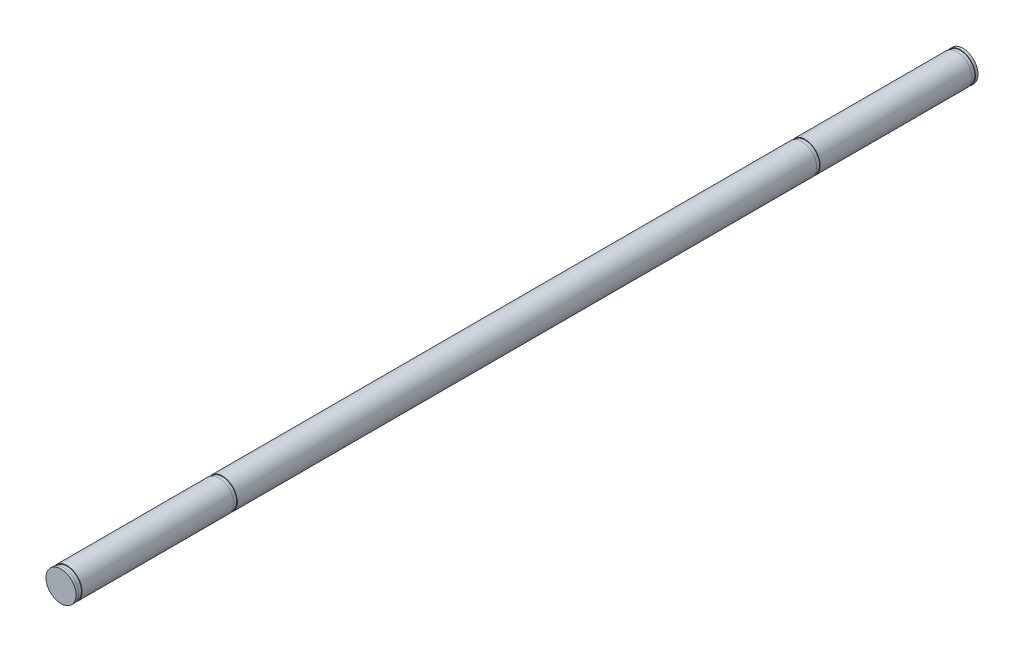
SolidWorks part; units mm, degrees
ref_plane "Front Plane" through (0, 0, 0) normal (0, 0, 1) x (1, 0, 0)
ref_plane "Top Plane" through (0, 0, 0) normal (0, 1, 0) x (1, 0, 0)
ref_plane "Right Plane" through (0, 0, 0) normal (1, 0, 0) x (0, 0, -1)
sketch "Sketch1" plane through (0, 0, 0) normal (0, 0, 1) x (1, 0, 0)
  circle A0 centre (0, 0) radius 5
  dimension "D1" = 10
extrude "Boss-Extrude1" add sketch "Sketch1" along normal mid plane 300
ref_plane "Plane1" through (0, 0, 148) normal (0, 0, 1) x (1, 0, 0)
ref_plane "Plane2" through (0, 0, 97.5) normal (0, 0, 1) x (1, 0, 0)
ref_plane "Plane3" through (0, 0, 55) normal (0, 0, 1) x (1, 0, 0)
sketch "Sketch2" plane through (0, 0, 148) normal (0, 0, 1) x (1, 0, 0)
  circle A0 centre (0, 0) radius 4.8
  circle A1 centre (0, 0) radius 5
  circle A2 centre (0, 0) radius 5
  dimension "D2" = 9.6
  dimension "D1" = 0
extrude "Cut-Extrude1" cut sketch "Sketch2" along normal blind 1.15
sketch "Sketch3" plane through (0, 0, 97.5) normal (0, 0, 1) x (1, 0, 0)
  circle A0 centre (0, 0) radius 5 construction
  circle A1 centre (0, 0) radius 4.8 construction
  circle A2 centre (0, 0) radius 5
  circle A3 centre (0, 0) radius 4.8
extrude "Cut-Extrude2" cut sketch "Sketch3" against normal blind 1.15
sketch "Sketch4" plane through (0, 0, 55) normal (0, 0, 1) x (1, 0, 0)
  circle A0 centre (0, 0) radius 4.5
  circle A1 centre (0, 0) radius 5
  circle A2 centre (0, 0) radius 5
  dimension "D2" = 9
  dimension "D1" = 0
extrude "Cut-Extrude3" [suppressed] cut sketch "Sketch4" against normal mid plane 2
mirror "Mirror1" about plane through (0, 0, 0) normal (0, 0, 1) of "Cut-Extrude3", "Cut-Extrude1", "Cut-Extrude2"
